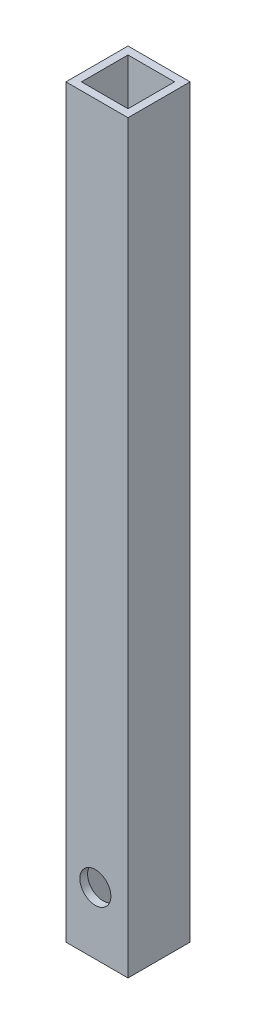
SolidWorks part; units mm, degrees
ref_plane "Front" through (0, 0, 0) normal (0, 0, 1) x (1, 0, 0)
ref_plane "Top" through (0, 0, 0) normal (0, 1, 0) x (1, 0, 0)
ref_plane "Right" through (0, 0, 0) normal (1, 0, 0) x (0, 0, -1)
sketch "Sketch1" plane through (0, 0, 0) normal (0, 1, 0) x (1, 0, 0)
  line L0 (1.5875, 1.5875) -> (11.1125, 1.5875)
  line L1 (0, 0) -> (12.7, 0)
  line L2 (0, 0) -> (0, 12.7)
  line L3 (0, 12.7) -> (12.7, 12.7)
  line L4 (12.7, 0) -> (12.7, 12.7)
  line L5 (11.1125, 1.5875) -> (11.1125, 11.1125)
  line L6 (1.5875, 11.1125) -> (11.1125, 11.1125)
  line L7 (1.5875, 1.5875) -> (1.5875, 11.1125)
  dimension "D1" = 1.5875
extrude "Boss-Extrude1" add sketch "Sketch1" along normal blind 152.4
sketch "Sketch2" plane through (0, 0, -12.7) normal (0, 0, -1) x (-1, 0, 0)
  circle A0 centre (-6.0223, 12.7) radius 3.175 construction
  circle A1 centre (-6.0223, 12.7) radius 3.175
extrude "Cut-Extrude1" cut sketch "Sketch2" against normal through all
